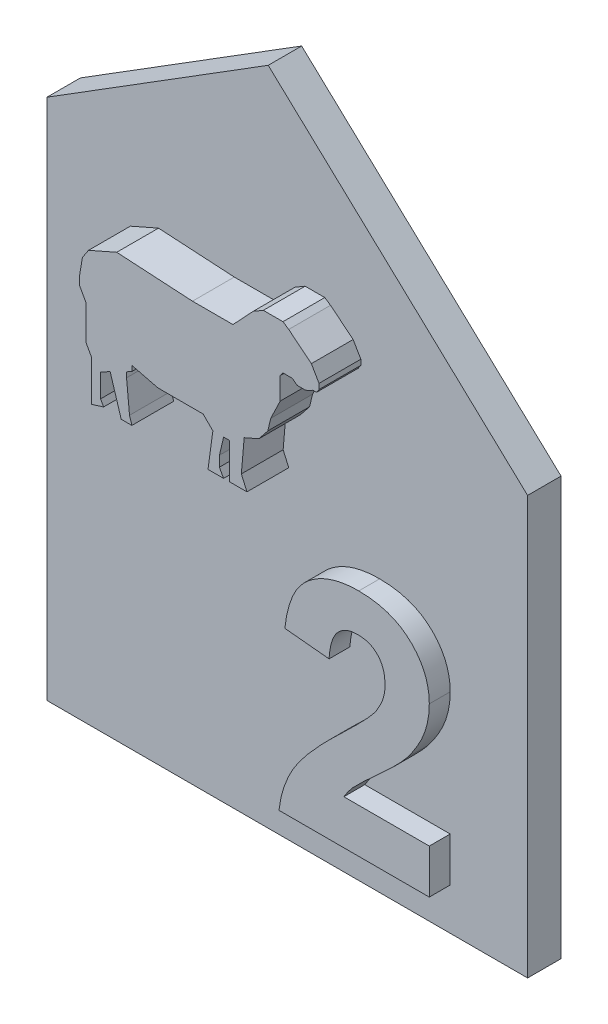
SolidWorks part; units mm, degrees
ref_plane "Přední rovina" through (0, 0, 0) normal (0, 0, 1) x (1, 0, 0)
ref_plane "Horní rovina" through (0, 0, 0) normal (0, 1, 0) x (1, 0, 0)
ref_plane "Pravá rovina" through (0, 0, 0) normal (1, 0, 0) x (0, 0, -1)
sketch "Skica1" plane through (0, 0, 0) normal (0, 0, 1) x (1, 0, 0)
  line L0 (-66.5051, 0) -> (66.5051, 0) construction
  line L1 (0, 0) -> (0, 20)
  line L2 (0, 20) -> (-12.4128, 31.6156)
  line L3 (-12.4128, 31.6156) -> (-23, 25)
  line L4 (-23, 25) -> (-23, 0)
  line L5 (-23, 0) -> (0, 0)
  dimension "D1" = 23
  dimension "D2" = 25
  dimension "D3" = 20
  dimension "D4" = 17
  dimension "D5" = 122
extrude "Přidat vysunutím5" add sketch "Skica1" along normal blind 1.6
sketch "Skica2" plane through (0, 0, 1.6) normal (0, 0, 1) x (1, 0, 0)
  line L1 (-23, 25) -> (-23, 0) construction
  line L2 (0, 0) -> (0, 20) construction
  line L3 (-3, 0) -> (-3, 22.8073) construction
  line L4 (-23, 0) -> (0, 0) construction
  line L5 (0, 20) -> (-12.4128, 31.6156) construction
  line L6 (-23, 2) -> (-3, 2) construction
  text T1 "2" font "Arial" height 11
  dimension "D2" = 3
  dimension "D3" = 2
extrude "Přidat vysunutím6" add sketch "Skica2" along normal blind 1
sketch "Sketch1" plane through (0, 0, 1.6) normal (0, 0, 1) x (1, 0, 0)
  line L0 (-21, 23.8113) -> (-21, 15)
  line L1 (-21, 23.8113) -> (-7, 23.8113)
  line L2 (-21, 15) -> (-7, 15)
  line L3 (-7, 23.8113) -> (-7, 15)
  line L4 (-23, 25) -> (-23, 0) construction
  line L6 (0, 20) -> (-12.4128, 31.6156) construction
  dimension "D1" = 2
  dimension "D2" = 2
  dimension "D3" = 14
  dimension "D4" = 2
extrude "Boss-Extrude1" add sketch "Sketch1" along normal blind 2
sketch "Sketch2" plane through (0, 0, 3.6) normal (0, 0, 1) x (1, 0, 0)
  line L0 (-21, 23.8113) -> (-21, 15) construction
  line L1 (-19.4447, 20.3589) -> (-19.4447, 19.9866)
  line L2 (-19.4447, 19.9866) -> (-19.1312, 19.4183)
  line L3 (-19.1312, 19.4183) -> (-19.1312, 18.0662)
  line L4 (-19.1312, 18.0662) -> (-19.1312, 17.7723)
  line L5 (-19.1312, 17.7723) -> (-18.8582, 17.2775)
  line L8 (-18.8582, 15.3424) -> (-18.2886, 15.5187)
  line L9 (-18.2886, 15.5187) -> (-18.4338, 15.7819)
  line L10 (-18.4338, 15.7819) -> (-18.4338, 16.8904)
  line L11 (-18.4338, 16.8904) -> (-17.9764, 17.1428)
  line L14 (-17.4463, 15.4306) -> (-16.9365, 15.4306)
  line L15 (-16.9365, 15.4306) -> (-17.0491, 15.7944)
  line L16 (-17.0491, 15.7944) -> (-17.1914, 17.2775)
  line L17 (-17.1914, 17.2775) -> (-17.1914, 17.5249)
  line L18 (-17.1914, 17.5249) -> (-16.9365, 17.6655)
  line L19 (-16.9365, 17.6655) -> (-16.9365, 17.9192)
  line L20 (-16.9365, 17.9192) -> (-16.427, 17.7924)
  line L21 (-16.427, 17.7924) -> (-15.689, 17.6087)
  line L26 (-13.5268, 17.6087) -> (-13.0609, 17.1428)
  line L27 (-13.0609, 17.1428) -> (-13.2939, 15.4306)
  line L28 (-13.2939, 15.4306) -> (-12.547, 15.4306)
  line L29 (-12.547, 15.4306) -> (-12.7477, 15.7944)
  line L30 (-12.7477, 15.7944) -> (-12.7477, 16.2867)
  line L31 (-12.7477, 16.2867) -> (-12.547, 17.1428)
  line L32 (-12.547, 17.1428) -> (-12.2531, 17.1428)
  line L33 (-12.2531, 17.1428) -> (-12.2531, 15.4306)
  line L34 (-12.2531, 15.4306) -> (-11.4301, 15.4306)
  line L35 (-11.4301, 15.4306) -> (-11.6978, 16.0405)
  line L36 (-11.6978, 16.0405) -> (-11.564, 17.6087)
  line L37 (-11.564, 17.6087) -> (-10.8566, 17.9192)
  line L38 (-10.8566, 17.9192) -> (-10.4307, 18.4581)
  line L39 (-10.4307, 18.4581) -> (-10.2932, 19.0447)
  line L40 (-10.2932, 19.0447) -> (-10.0192, 19.6143)
  line L41 (-10.0192, 19.6143) -> (-9.8401, 19.9866)
  line L42 (-9.8401, 19.9866) -> (-9.8401, 20.5744)
  line L43 (-9.8401, 20.5744) -> (-9.8401, 21.0447)
  line L44 (-9.8401, 21.0447) -> (-9.7056, 21.2211)
  line L45 (-9.7056, 21.2211) -> (-9.4313, 21.2211)
  line L46 (-9.4313, 21.2211) -> (-9.2549, 21.2211)
  line L47 (-9.2549, 21.2211) -> (-9.0236, 21.0447)
  line L48 (-9.0236, 21.0447) -> (-8.6279, 21.0447)
  line L49 (-8.6279, 21.0447) -> (-8.427, 21.1329)
  line L50 (-8.427, 21.1329) -> (-8.2752, 21.2211)
  line L51 (-8.2752, 21.2211) -> (-8.0988, 21.2211)
  line L52 (-8.0988, 21.2211) -> (-7.9812, 21.3975)
  line L53 (-7.9812, 21.3975) -> (-7.9812, 21.6522)
  line L54 (-7.9812, 21.6522) -> (-8.3487, 22.285)
  line L59 (-9.4313, 23.1619) -> (-9.7056, 23.3447)
  line L63 (-10.6462, 23.3447) -> (-11.1289, 23.0645)
  line L64 (-11.1289, 23.0645) -> (-11.6978, 22.4571)
  line L65 (-11.6978, 22.4571) -> (-12.098, 22.0298)
  line L66 (-12.098, 22.0298) -> (-12.547, 22.0298)
  line L67 (-12.547, 22.0298) -> (-14.0363, 22.0298)
  line L68 (-14.0363, 22.0298) -> (-17.6615, 22.2434)
  line L69 (-17.6615, 22.2434) -> (-18.616, 21.8244)
  line L70 (-18.616, 21.8244) -> (-19.0083, 21.6522)
  line L71 (-19.0083, 21.6522) -> (-19.3023, 21.2111)
  line L72 (-19.3023, 21.2111) -> (-19.4447, 20.3589)
  line L73 (-9.4313, 23.1619) -> (-8.3487, 22.285)
  line L74 (-10.6462, 23.3447) -> (-9.7056, 23.3447)
  line L75 (-15.689, 17.6087) -> (-13.5268, 17.6087)
  line L76 (-18.8582, 15.3424) -> (-18.8582, 17.2775)
  line L77 (-17.9764, 17.1428) -> (-17.4463, 15.4306)
  line L78 (-7, 23.8113) -> (-21, 23.8113) construction
  line L79 (-21, 15) -> (-21, 23.8113)
  line L80 (-21, 23.8113) -> (-7, 23.8113)
  line L81 (-7, 23.8113) -> (-7, 15)
  line L82 (-7, 15) -> (-21, 15)
  line M1 (-7, 23.8113) -> (-21, 23.8113)
  line M2 (-21, 23.8113) -> (-21, 15)
  line M3 (-21, 15) -> (-7, 15)
  line M4 (-7, 15) -> (-7, 23.8113)
  dimension "D1" = 1.5553
  dimension "D2" = 1.6977
  dimension "D3" = 1.8688
  dimension "D4" = 1.9917
  dimension "D5" = 2.1418
  dimension "D6" = 2.384
  dimension "D7" = 2.5662
  dimension "D8" = 2.7114
  dimension "D9" = 3.0236
  dimension "D10" = 3.3385
  dimension "D11" = 3.5537
  dimension "D12" = 3.8086
  dimension "D13" = 3.9509
  dimension "D14" = 4.0635
  dimension "D15" = 4.573
  dimension "D16" = 5.311
  dimension "D17" = 6.9637
  dimension "D18" = 7.4732
  dimension "D19" = 7.7061
  dimension "D20" = 7.9391
  dimension "D21" = 8.2523
  dimension "D22" = 8.453
  dimension "D23" = 8.7469
  dimension "D24" = 8.902
  dimension "D25" = 9.3022
  dimension "D26" = 9.436
  dimension "D27" = 9.5699
  dimension "D28" = 9.8711
  dimension "D29" = 10.1434
  dimension "D30" = 10.3538
  dimension "D31" = 10.5693
  dimension "D32" = 10.7068
  dimension "D33" = 10.9808
  dimension "D34" = 11.1599
  dimension "D35" = 11.2944
  dimension "D36" = 11.5687
  dimension "D37" = 11.7451
  dimension "D38" = 11.9764
  dimension "D39" = 12.3721
  dimension "D40" = 12.573
  dimension "D41" = 12.6513
  dimension "D42" = 12.7248
  dimension "D43" = 0.4666
  dimension "D44" = 13.0188
  dimension "D45" = 14
  dimension "D46" = 0.6495
  dimension "D47" = 0.7468
  dimension "D48" = 1.3543
  dimension "D49" = 1.5263
  dimension "D50" = 2.4139
  dimension "D51" = 3.4525
  dimension "D52" = 3.8248
  dimension "D53" = 4.1971
  dimension "D54" = 4.3931
  dimension "D55" = 5.3532
  dimension "D56" = 5.7452
  dimension "D57" = 5.8921
  dimension "D58" = 6.1458
  dimension "D59" = 3.2369
  dimension "D60" = 6.6686
  dimension "D61" = 8.0294
extrude "Cut-Extrude1" cut sketch "Sketch2" against normal blind 2 contours L77 L11 L10 L9 L8 L76 L5 L4 L3 L2 L1 L72 L71 L70 L69 L68 L67 L66 L65 L64 L63 L74 L59 L73 L54 L53 L52 L51 L50 L49 L48 L47 L46 L45 L44 L43 L42 L41 L40 L39 L38 L37 L36 L35 L34 L33 M4 M1 M2 M3
